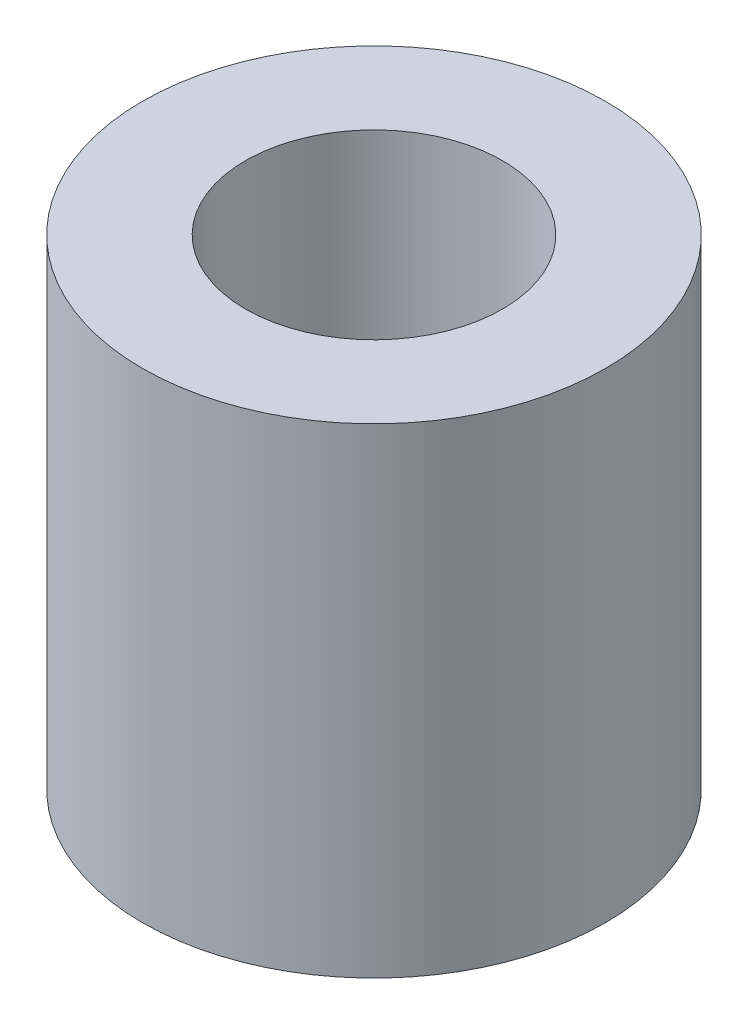
SolidWorks part; units mm, degrees
ref_plane "Plano frontal" through (0, 0, 0) normal (0, 0, 1) x (1, 0, 0)
ref_plane "Plano superior" through (0, 0, 0) normal (0, 1, 0) x (1, 0, 0)
ref_plane "Plano direito" through (0, 0, 0) normal (1, 0, 0) x (0, 0, -1)
sketch "Esboço1" plane through (0, 0, 0) normal (0, 1, 0) x (1, 0, 0)
  circle A0 centre (0, 0) radius 1.875
  circle A2 centre (0, 0) radius 3.375
  dimension "D1" = 3.75
  dimension "D2" = 1.5
extrude "Ressalto-extrusão1" add sketch "Esboço1" along normal blind 7
